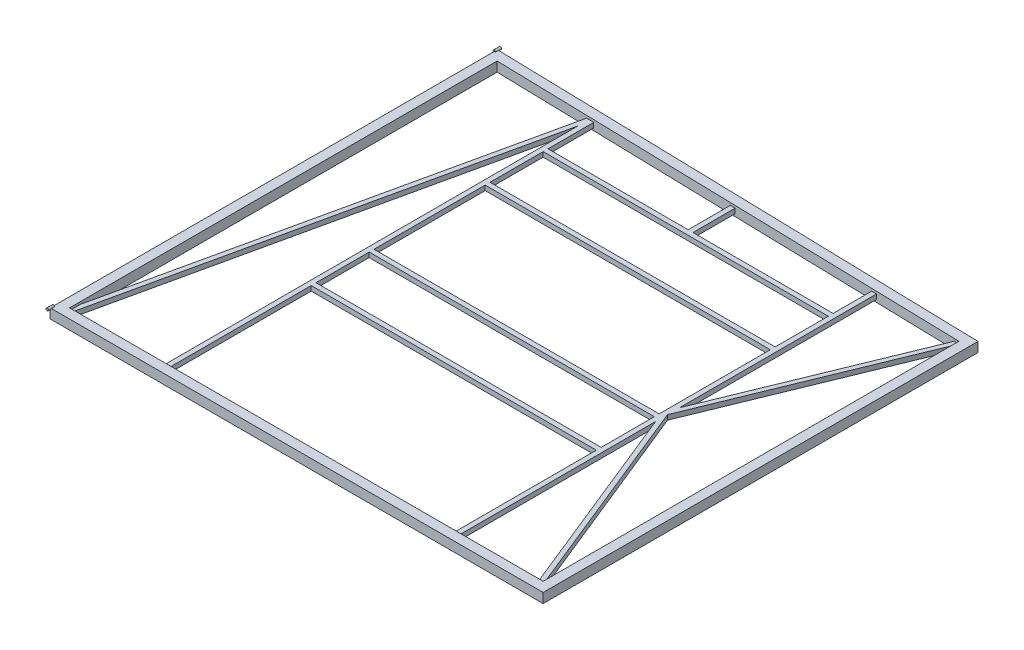
SolidWorks part; units mm, degrees
material "6063-T6"
ref_plane "Front Plane" through (0, 0, 0) normal (0, 0, 1) x (1, 0, 0)
ref_plane "Top Plane" through (0, 0, 0) normal (0, 1, 0) x (1, 0, 0)
ref_plane "Right Plane" through (0, 0, 0) normal (1, 0, 0) x (0, 0, -1)
sketch "Sketch1" plane through (0, 0, 0) normal (0, 1, 0) x (1, 0, 0)
  line L0 (0, 2298.7) -> (0, 0)
  line L1 (0, 0) -> (2540, 0)
  line L2 (2540, 0) -> (2540, 2235.2)
  line L3 (2540, 2235.2) -> (0, 2298.7)
  dimension "D1" = 2235.2
  dimension "D2" = 2540
  dimension "D3" = 2298.7
ref_plane "Plane1" through (0, 0, -1016) normal (0, 0, 1) x (1, 0, 0)
sketch "Sketch2" plane through (0, 0, -1016) normal (0, 0, 1) x (1, 0, 0)
  line L0 (-22.225, 22.225) -> (-22.225, -22.225)
  line L1 (-25.4, 25.4) -> (25.4, 25.4)
  line L2 (-25.4, 25.4) -> (-25.4, -25.4)
  line L3 (-25.4, -25.4) -> (25.4, -25.4)
  line L4 (25.4, 25.4) -> (25.4, -25.4)
  line L5 (-25.4, 25.4) -> (25.4, -25.4) construction
  line L6 (-25.4, -25.4) -> (25.4, 25.4) construction
  line L7 (-22.225, -22.225) -> (22.225, -22.225)
  line L8 (22.225, 22.225) -> (22.225, -22.225)
  line L9 (-22.225, 22.225) -> (22.225, 22.225)
  point P0 (0, 0)
  dimension "D1" = 50.8
  dimension "D2" = 50.8
  dimension "D3" = 3.175
sweep "Sweep1" add profiles "Sketch2" path "Sketch1"
sketch "Sketch3" plane through (0, 0, -25.4) normal (0, 0, -1) x (-1, 0, 0)
  line L0 (-520.7, -12.7) -> (-520.7, 12.7)
  line L1 (-2044.7, -12.7) -> (-2070.1, -12.7)
  line L2 (-2044.7, -12.7) -> (-2044.7, 12.7)
  line L3 (-2044.7, 12.7) -> (-2070.1, 12.7)
  line L4 (-2070.1, -12.7) -> (-2070.1, 12.7)
  line L5 (-2044.7, -12.7) -> (-2070.1, 12.7) construction
  line L6 (-2044.7, 12.7) -> (-2070.1, -12.7) construction
  line L7 (-2514.6, 25.4) -> (-2514.6, -25.4) construction
  line L8 (-2066.925, -9.525) -> (-2066.925, 9.525)
  line L9 (-2047.875, 9.525) -> (-2066.925, 9.525)
  line L10 (-2047.875, -9.525) -> (-2047.875, 9.525)
  line L11 (-2047.875, -9.525) -> (-2066.925, -9.525)
  line L12 (-2514.6, -25.4) -> (-25.4, -25.4) construction
  line L17 (-520.7, -12.7) -> (-546.1, -12.7)
  line L18 (-546.1, -12.7) -> (-546.1, 12.7)
  line L23 (-520.7, 12.7) -> (-546.1, 12.7)
  line L24 (-542.925, -9.525) -> (-542.925, 9.525)
  line L25 (-523.875, 9.525) -> (-542.925, 9.525)
  line L26 (-523.875, -9.525) -> (-523.875, 9.525)
  line L27 (-523.875, -9.525) -> (-542.925, -9.525)
  line L28 (-25.4, 25.4) -> (-25.4, -25.4) construction
  point P0 (-2057.4, 0)
  point P5 (-533.4, 12.7)
  point P20 (-2514.6, 0)
  dimension "D1" = 25.4
  dimension "D2" = 25.4
  dimension "D3" = 25.4
  dimension "D5" = 457.2
  dimension "D6" = 2
  dimension "D7" = 508
  dimension "D4" = 3.175
extrude "Boss-Extrude1" add sketch "Sketch3" along normal up to surface (2196.1396 mm away)
sketch "Sketch4" plane through (546.1, 0, 0) normal (1, 0, 0) x (0, 0, -1)
  line L0 (2259.6396, -12.7) -> (25.4, -12.7) construction
  line L1 (800.1, 12.7) -> (774.7, 12.7)
  line L2 (800.1, 12.7) -> (800.1, -12.7)
  line L3 (800.1, -12.7) -> (774.7, -12.7)
  line L4 (774.7, 12.7) -> (774.7, -12.7)
  line L5 (800.1, 12.7) -> (774.7, -12.7) construction
  line L6 (800.1, -12.7) -> (774.7, 12.7) construction
  line L7 (25.4, 12.7) -> (25.4, -12.7) construction
  line L8 (1104.9, 12.7) -> (1079.5, 12.7)
  line L9 (1104.9, 12.7) -> (1104.9, -12.7)
  line L10 (1104.9, -12.7) -> (1079.5, -12.7)
  line L11 (1079.5, 12.7) -> (1079.5, -12.7)
  line L12 (1104.9, 12.7) -> (1079.5, -12.7) construction
  line L13 (1104.9, -12.7) -> (1079.5, 12.7) construction
  line L14 (796.925, 9.525) -> (796.925, -9.525)
  line L15 (2259.6396, 12.7) -> (25.4, 12.7) construction
  line L16 (1714.5, 12.7) -> (1689.1, 12.7)
  line L17 (1714.5, 12.7) -> (1714.5, -12.7)
  line L18 (1714.5, -12.7) -> (1689.1, -12.7)
  line L19 (1689.1, 12.7) -> (1689.1, -12.7)
  line L20 (1714.5, 12.7) -> (1689.1, -12.7) construction
  line L21 (1714.5, -12.7) -> (1689.1, 12.7) construction
  line L22 (2019.3, 12.7) -> (1993.9, 12.7)
  line L23 (2019.3, 12.7) -> (2019.3, -12.7)
  line L24 (2019.3, -12.7) -> (1993.9, -12.7)
  line L25 (1993.9, 12.7) -> (1993.9, -12.7)
  line L26 (2019.3, 12.7) -> (1993.9, -12.7) construction
  line L27 (2019.3, -12.7) -> (1993.9, 12.7) construction
  line L28 (796.925, -9.525) -> (777.875, -9.525)
  line L29 (777.875, 9.525) -> (777.875, -9.525)
  line L30 (796.925, 9.525) -> (777.875, 9.525)
  line L31 (1101.725, 9.525) -> (1101.725, -9.525)
  line L32 (1101.725, -9.525) -> (1082.675, -9.525)
  line L33 (1082.675, 9.525) -> (1082.675, -9.525)
  line L34 (1101.725, 9.525) -> (1082.675, 9.525)
  line L35 (1711.325, 9.525) -> (1692.275, 9.525)
  line L36 (1692.275, 9.525) -> (1692.275, -9.525)
  line L37 (1711.325, -9.525) -> (1692.275, -9.525)
  line L38 (1711.325, 9.525) -> (1711.325, -9.525)
  line L39 (2016.125, 9.525) -> (1997.075, 9.525)
  line L40 (1997.075, 9.525) -> (1997.075, -9.525)
  line L41 (2016.125, -9.525) -> (1997.075, -9.525)
  line L42 (2016.125, 9.525) -> (2016.125, -9.525)
  point P0 (787.4, 0)
  point P7 (1092.2, 0)
  point P16 (1701.8, 0)
  point P21 (2006.6, 0)
  dimension "D1" = 25.4
  dimension "D2" = 25.4
  dimension "D3" = 304.8
  dimension "D4" = 762
  dimension "D5" = 25.4
  dimension "D6" = 25.4
  dimension "D7" = 304.8
  dimension "D8" = 609.6
  dimension "D9" = 3.175
  dimension "D10" = 3.175
  dimension "D11" = 3.175
  dimension "D12" = 3.175
extrude "Boss-Extrude2" add sketch "Sketch4" along normal up to surface (1498.6 mm away) up to face at (2044.7, 0, -1123.7873)
sketch "Sketch5" plane through (0, 0, -25.4) normal (0, 0, -1) x (-1, 0, 0)
  line L1 (-12.7, -12.7) -> (-38.1, -12.7)
  line L2 (-12.7, -12.7) -> (-12.7, 12.7)
  line L3 (-12.7, 12.7) -> (-38.1, 12.7)
  line L4 (-38.1, -12.7) -> (-38.1, 12.7)
  line L5 (-12.7, -12.7) -> (-38.1, 12.7) construction
  line L6 (-12.7, 12.7) -> (-38.1, -12.7) construction
  line L7 (-520.7, 12.7) -> (-546.1, 12.7) construction
  line L8 (-546.1, -12.7) -> (-520.7, -12.7) construction
  line L9 (-15.875, -9.525) -> (-15.875, 9.525)
  line L10 (-15.875, 9.525) -> (-34.925, 9.525)
  line L11 (-34.925, -9.525) -> (-34.925, 9.525)
  line L12 (-15.875, -9.525) -> (-34.925, -9.525)
  line L13 (-25.4, 25.4) -> (-25.4, -25.4) construction
  point P0 (-25.4, 0)
  point P16 (-25.4, 0)
  dimension "D1" = 25.4
  dimension "D2" = 3.175
sketch "Sketch6" plane through (0, 25.4, 0) normal (0, 1, 0) x (1, 0, 0)
  line L0 (25.4, 25.4) -> (520.7, 2260.2746)
sweep "Sweep2" add profiles "Sketch5" path "Sketch6"
sketch "Sketch11" plane through (0, 0, -2019.3) normal (0, 0, -1) x (-1, 0, 0)
  line L0 (-2044.7, -12.7) -> (-546.1, -12.7) construction
  line L1 (-1282.7, -12.7) -> (-1308.1, -12.7)
  line L2 (-1282.7, -12.7) -> (-1282.7, 12.7)
  line L3 (-1282.7, 12.7) -> (-1308.1, 12.7)
  line L4 (-1308.1, -12.7) -> (-1308.1, 12.7)
  line L5 (-1282.7, -12.7) -> (-1308.1, 12.7) construction
  line L6 (-1282.7, 12.7) -> (-1308.1, -12.7) construction
  line L7 (-2044.7, 12.7) -> (-546.1, 12.7) construction
  line L9 (-1285.875, -9.525) -> (-1285.875, 9.525)
  line L10 (-1285.875, 9.525) -> (-1304.925, 9.525)
  line L11 (-1304.925, -9.525) -> (-1304.925, 9.525)
  line L12 (-1285.875, -9.525) -> (-1304.925, -9.525)
  line L13 (-2044.7, 12.7) -> (-546.1, 12.7) construction
  point P12 (-1295.4, 12.7)
  point P20 (-1295.4, 0)
  dimension "D1" = 25.4
  dimension "D2" = 3.175
extrude "Boss-Extrude3" add sketch "Sketch11" along normal up to surface (221.2896 mm away)
sketch "Sketch13" plane through (0, 0, -25.4) normal (0, 0, -1) x (-1, 0, 0)
  line L0 (-2514.6, 25.4) -> (-2514.6, -25.4) construction
  line L1 (-2489.2, -12.7) -> (-2514.6, -12.7)
  line L2 (-2489.2, -12.7) -> (-2489.2, 12.7)
  line L3 (-2489.2, 12.7) -> (-2514.6, 12.7)
  line L4 (-2514.6, -12.7) -> (-2514.6, 12.7)
  line L5 (-2489.2, -12.7) -> (-2514.6, 12.7) construction
  line L6 (-2489.2, 12.7) -> (-2514.6, -12.7) construction
  line L7 (-2492.375, -9.525) -> (-2492.375, 9.525)
  line L8 (-2492.375, 9.525) -> (-2511.425, 9.525)
  line L9 (-2511.425, -9.525) -> (-2511.425, 9.525)
  line L10 (-2492.375, -9.525) -> (-2511.425, -9.525)
  point P0 (-2501.9, 0)
  point P8 (-2514.6, 0)
  dimension "D1" = 25.4
  dimension "D2" = 25.4
  dimension "D3" = 3.175
sketch "Sketch14" plane through (0, 25.4, 0) normal (0, 1, 0) x (1, 0, 0)
  line L0 (2514.6, 25.4) -> (2070.1, 1123.4698)
  line L1 (2070.1, 2221.5396) -> (2070.1, 25.4) construction
  line L2 (2070.1, 1123.4698) -> (2514.6, 2210.4271)
sweep "Sweep6" add profiles "Sketch13" path "Sketch14"
ref_plane "NORMAL PIN PLANE" through (0, 0, -2324.7429) normal (0, 0, 1) x (1, 0, 0)
sketch "Sketch15" plane through (0, 0, -2324.7429) normal (0, 0, 1) x (1, 0, 0)
  circle A0 centre (-25.4, 25.4) radius 6.35
  dimension "D1" = 12.7
extrude "Boss-Extrude4" add sketch "Sketch15" along normal mid plane 31.75
sketch "Sketch16" plane through (0, 0, 25.4) normal (0, 0, 1) x (1, 0, 0)
  circle A0 centre (-25.4, 25.4) radius 6.35
  dimension "D1" = 12.7
extrude "Boss-Extrude5" add sketch "Sketch16" along normal mid plane 31.75
